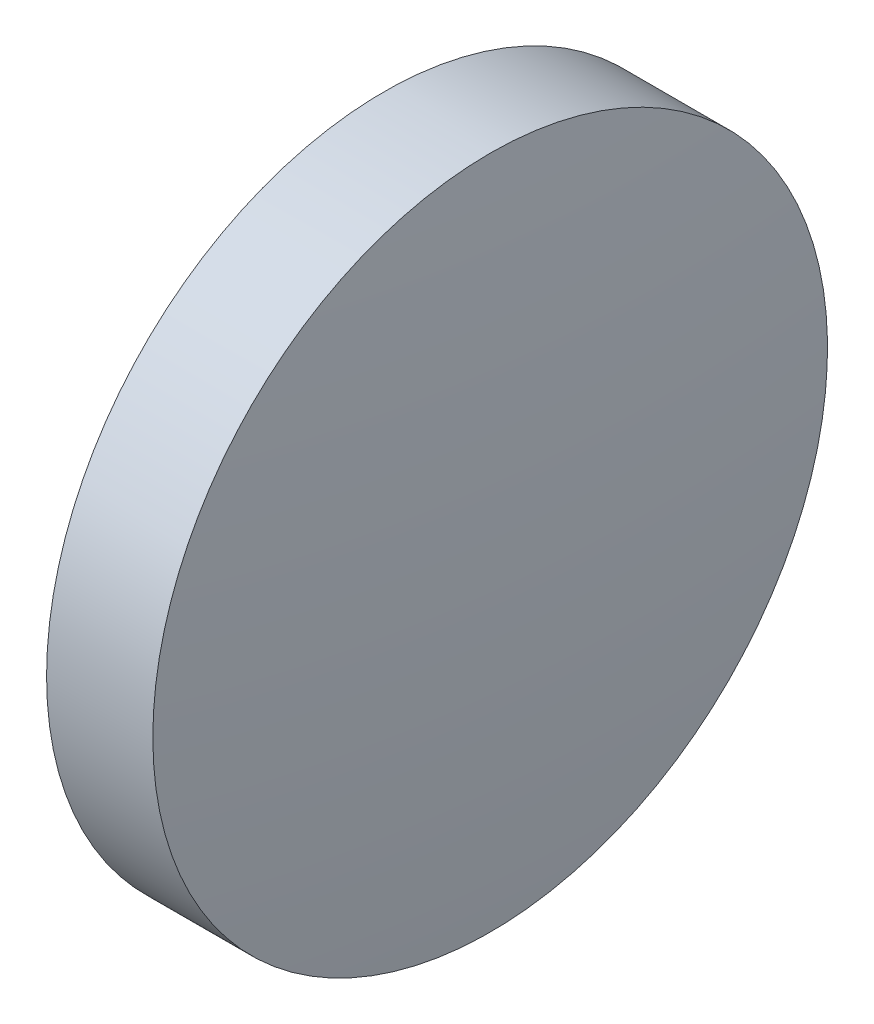
SolidWorks part; units mm, degrees
ref_plane "前视基准面" through (0, 0, 0) normal (0, 0, 1) x (1, 0, 0)
ref_plane "上视基准面" through (0, 0, 0) normal (0, 1, 0) x (1, 0, 0)
ref_plane "右视基准面" through (0, 0, 0) normal (1, 0, 0) x (0, 0, -1)
sketch "草图1" plane through (0, 0, 0) normal (0, 0, 1) x (1, 0, 0)
  line L0 (44.0661, 26.0934) -> (51.5845, 26.0934) construction
  line L1 (46.3026, 26.0934) -> (46.3026, 32.4434)
  line L2 (46.3026, 32.4434) -> (48.3026, 32.4434)
  line L3 (48.6026, 26.0934) -> (46.3026, 26.0934)
  arc A0 (48.6026, 26.0934) -> (48.3026, 32.4434) centre (-18.7516, 26.0934) ccw
revolve "旋转1" add sketch "草图1" angle 360 about L0
